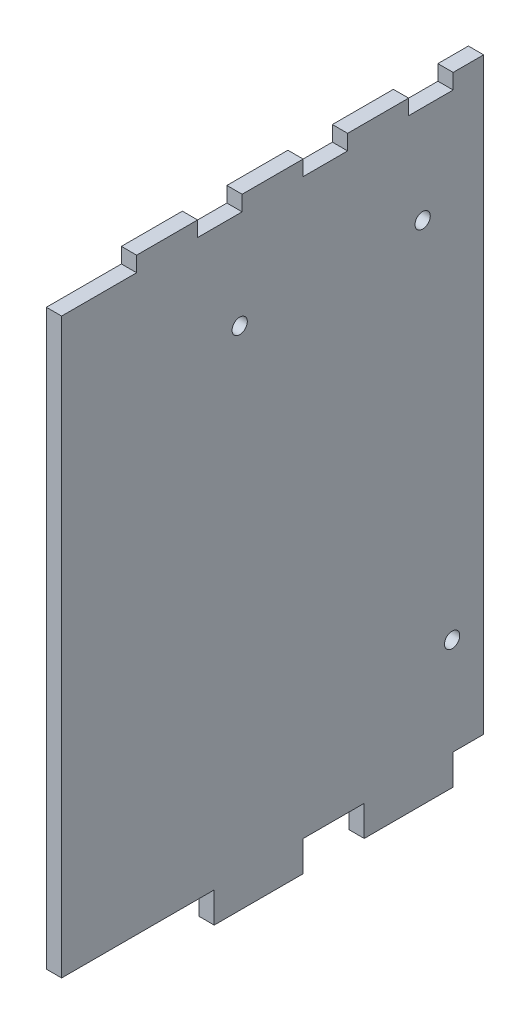
SolidWorks part; units mm, degrees
ref_plane "Front Plane" through (0, 0, 0) normal (0, 0, 1) x (1, 0, 0)
ref_plane "Top Plane" through (0, 0, 0) normal (0, 1, 0) x (1, 0, 0)
ref_plane "Right Plane" through (0, 0, 0) normal (1, 0, 0) x (0, 0, -1)
sketch "Sketch1" plane through (0, 0, 0) normal (1, 0, 0) x (0, 0, -1)
  line L1 (0, 119.38) -> (15.621, 119.38)
  line L2 (0, 119.38) -> (0, 0)
  line L3 (0, 0) -> (31.7754, 0)
  line L4 (87.884, 122.555) -> (87.884, 0)
  line L6 (31.7754, 0) -> (31.7754, -6.35)
  line L7 (31.7754, -6.35) -> (50.2666, -6.35)
  line L8 (50.2666, 0) -> (50.2666, -6.35)
  line L9 (63.0174, 0) -> (63.0174, -6.35)
  line L10 (63.0174, -6.35) -> (81.5086, -6.35)
  line L11 (81.5086, 0) -> (81.5086, -6.35)
  line L12 (50.2666, 0) -> (63.0174, 0)
  line L13 (81.5086, 0) -> (87.884, 0)
  line L16 (15.621, 119.38) -> (15.621, 122.555)
  line L17 (15.621, 122.555) -> (28.321, 122.555)
  line L18 (28.321, 119.38) -> (28.321, 122.555)
  line L19 (37.592, 119.38) -> (37.592, 122.555)
  line L20 (37.592, 122.555) -> (50.292, 122.555)
  line L21 (50.292, 119.38) -> (50.292, 122.555)
  line L23 (59.563, 119.38) -> (59.563, 122.555)
  line L24 (59.563, 122.555) -> (72.263, 122.555)
  line L25 (72.263, 119.38) -> (72.263, 122.555)
  line L26 (28.321, 119.38) -> (37.592, 119.38)
  line L27 (50.292, 119.38) -> (59.563, 119.38)
  line L28 (72.263, 119.38) -> (81.534, 119.38)
  line L29 (87.884, 122.555) -> (81.534, 122.555)
  line L33 (81.534, 119.38) -> (81.534, 122.555)
  point P13 (41.021, -6.35)
  point P26 (72.263, -6.35)
  point P28 (21.971, 122.555)
  point P30 (43.942, 122.555)
  point P31 (65.913, 122.555)
  point P32 (84.709, 122.555)
  dimension "D3" = 12.7
  dimension "D1" = 119.38
  dimension "D2" = 3.175
  dimension "D4" = 31.242
  dimension "D5" = 18.4912
  dimension "D7" = 6.3754
  dimension "D8" = 31.7754
  dimension "D9" = 6.35
  dimension "D10" = 15.621
  dimension "D11" = 3
  dimension "D12" = 21.971
  dimension "D13" = 3.175
  dimension "D14" = 18.796
  dimension "D6" = 2
extrude "Boss-Extrude1" add sketch "Sketch1" along normal blind 3.175
sketch "Sketch2" plane through (3.175, 0, 0) normal (1, 0, 0) x (0, 0, -1)
  line L0 (37.592, 119.38) -> (28.321, 119.38) construction
  line L1 (87.884, 0) -> (87.884, 122.555) construction
  circle A0 centre (37.084, 99.06) radius 1.5875
  circle A1 centre (75.184, 99.06) radius 1.5875
  dimension "D1" = 3.175
  dimension "D2" = 3.175
  dimension "D3" = 20.32
  dimension "D4" = 38.1
  dimension "D5" = 12.7
extrude "Cut-Extrude1" cut sketch "Sketch2" against normal through all
sketch "Sketch3" plane through (0, 0, 0) normal (-1, 0, 0) x (0, 0, 1)
  circle A0 centre (-81.32, 20.32) radius 1.5875
extrude "Cut-Extrude2" cut sketch "Sketch3" against normal through all
